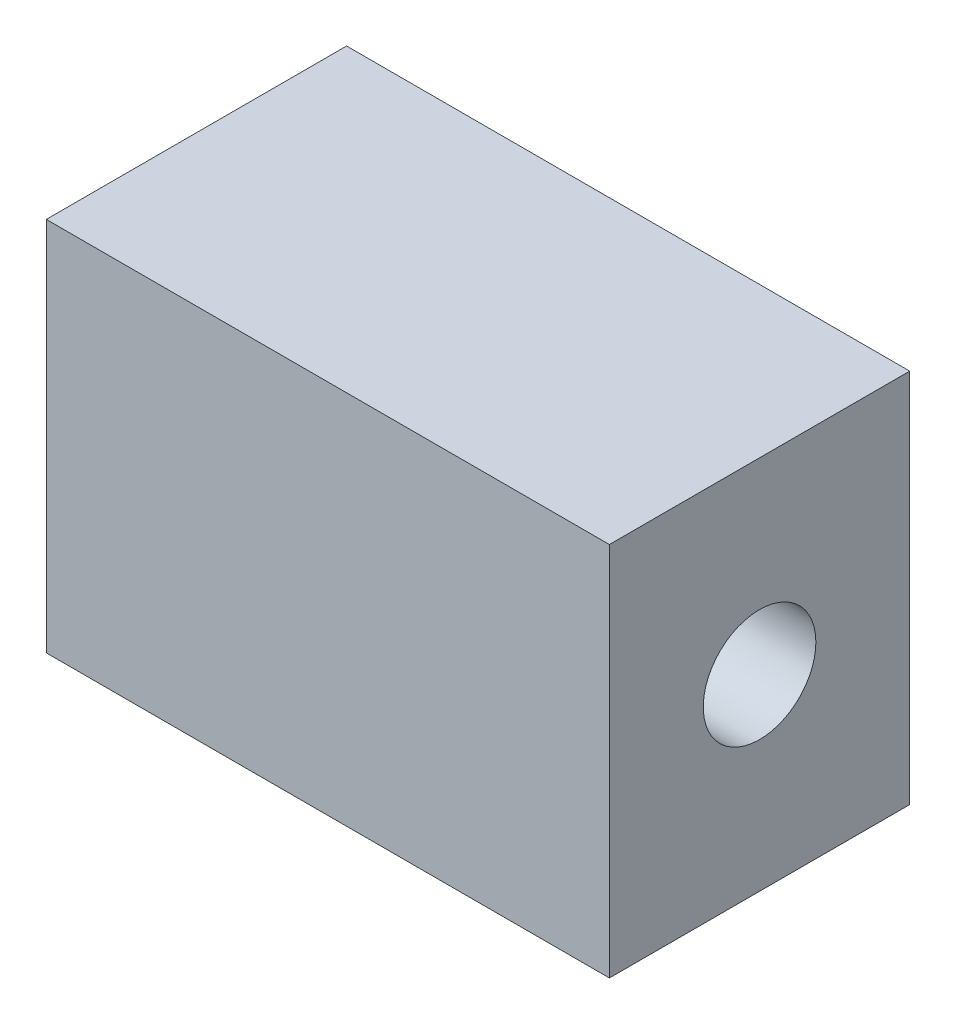
SolidWorks part; units mm, degrees
ref_plane "Front Plane" through (0, 0, 0) normal (0, 0, 1) x (1, 0, 0)
ref_plane "Top Plane" through (0, 0, 0) normal (0, 1, 0) x (1, 0, 0)
ref_plane "Right Plane" through (0, 0, 0) normal (1, 0, 0) x (0, 0, -1)
sketch "Sketch1" plane through (0, 0, 0) normal (0, 0, 1) x (1, 0, 0)
  line L1 (-11.6376, 9.4978) -> (3.3624, 9.4978)
  line L2 (-11.6376, 9.4978) -> (-11.6376, -0.5022)
  line L3 (-11.6376, -0.5022) -> (3.3624, -0.5022)
  line L4 (3.3624, 9.4978) -> (3.3624, -0.5022)
  dimension "D1" = 10
  dimension "D2" = 15
extrude "Boss-Extrude2" add sketch "Sketch1" along normal blind 8 contours L2 L1 L4 L3
sketch "Sketch2" plane through (3.3624, 0, 0) normal (1, 0, 0) x (0, 0, -1)
  circle A0 centre (-4, 4.4978) radius 1.5
  dimension "D1" = 3
extrude "Cut-Extrude1" cut sketch "Sketch2" against normal blind 15
